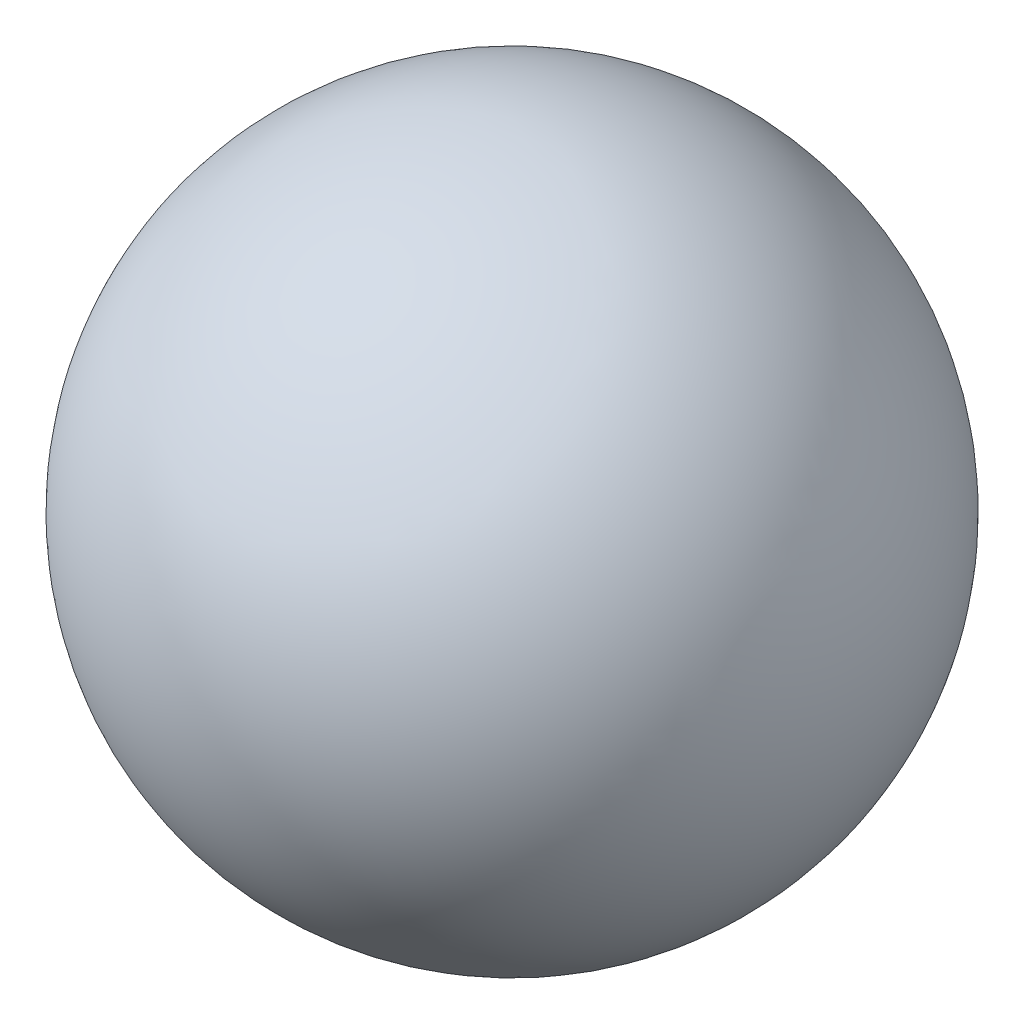
SolidWorks part; units mm, degrees
ref_plane "Front Plane" through (0, 0, 0) normal (0, 0, 1) x (1, 0, 0)
ref_plane "Top Plane" through (0, 0, 0) normal (0, 1, 0) x (1, 0, 0)
ref_plane "Right Plane" through (0, 0, 0) normal (1, 0, 0) x (0, 0, -1)
ref_plane "Plane1" through (0, 0, 3.827) normal (0, 0, 1) x (1, 0, 0)
sketch "Sketch1" plane through (0, 0, 3.827) normal (0, 0, 1) x (1, 0, 0)
  line L0 (12.882, 9.239) -> (8.118, 9.239)
  line L1 (50, 9.239) -> (-50, 9.239) construction
  arc A0 (8.118, 9.239) -> (12.882, 9.239) centre (10.5, 9.239) cw
revolve "Revolve1" add sketch "Sketch1" angle 360 about L1
